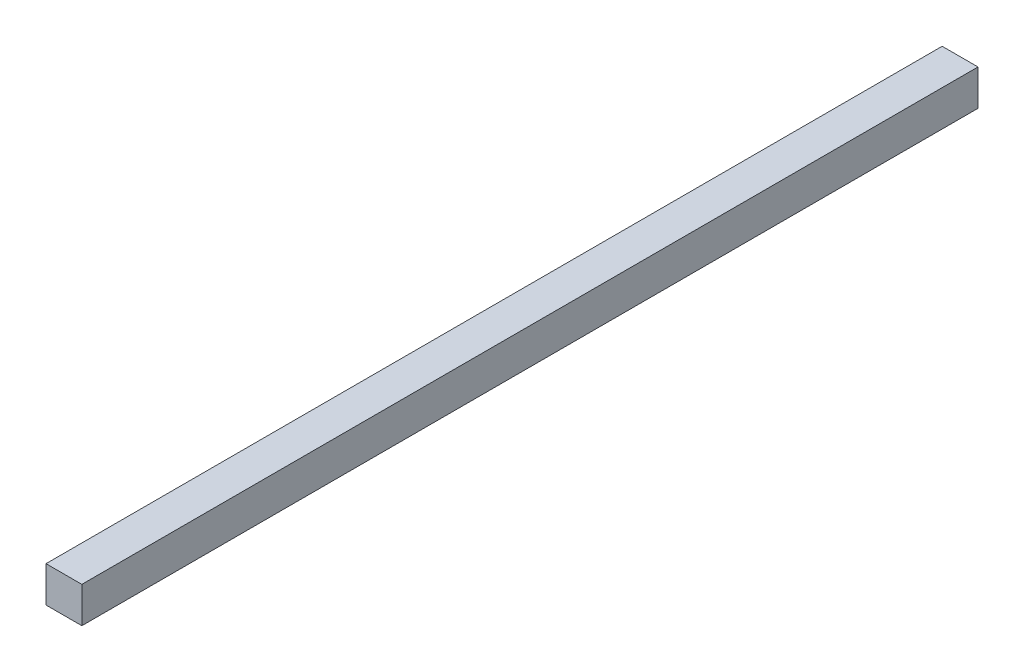
SolidWorks part; units mm, degrees
ref_plane "前视基准面" through (0, 0, 0) normal (0, 0, 1) x (1, 0, 0)
ref_plane "上视基准面" through (0, 0, 0) normal (0, 1, 0) x (1, 0, 0)
ref_plane "右视基准面" through (0, 0, 0) normal (1, 0, 0) x (0, 0, -1)
sketch "草图1" plane through (0, 0, 0) normal (0, 0, 1) x (1, 0, 0)
  line L1 (-10, -10) -> (10, -10)
  line L2 (-10, -10) -> (-10, 10)
  line L3 (-10, 10) -> (10, 10)
  line L4 (10, -10) -> (10, 10)
  line L5 (-10, -10) -> (10, 10) construction
  line L6 (-10, 10) -> (10, -10) construction
  point P0 (0, 0)
  dimension "D1" = 20
  dimension "D2" = 20
extrude "凸台-拉伸1" add sketch "草图1" along normal blind 500
